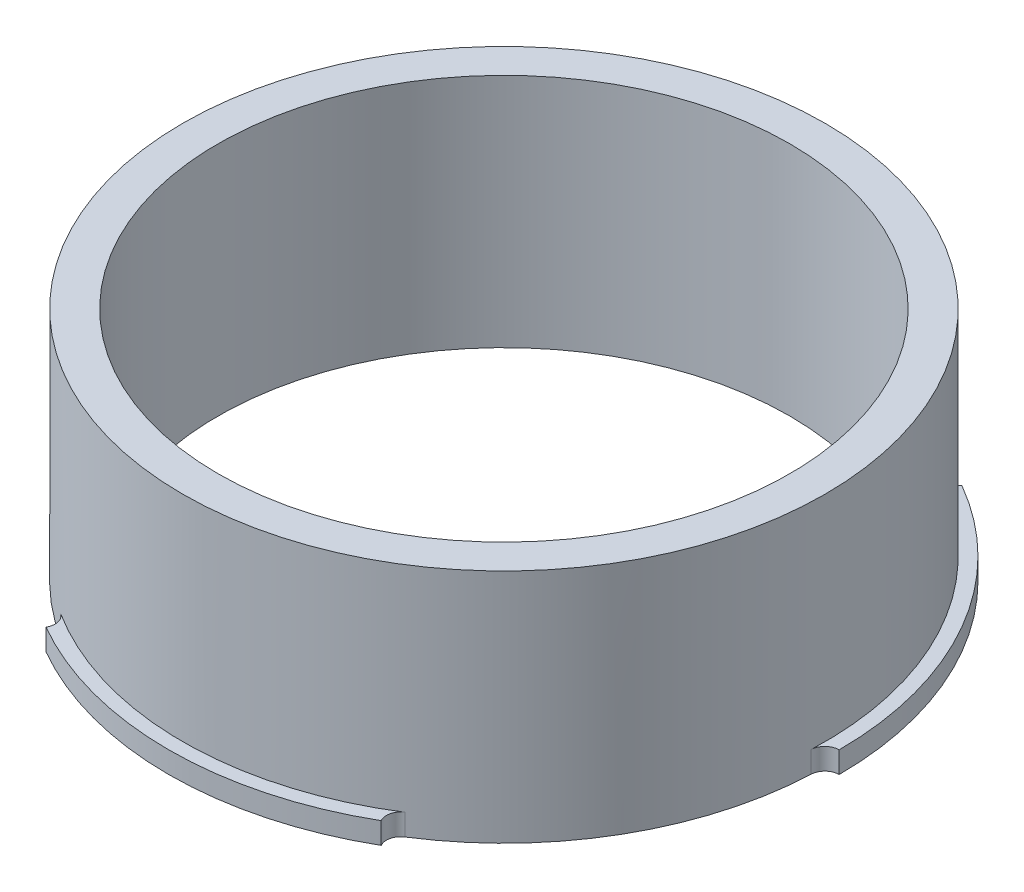
SolidWorks part; units mm, degrees
ref_plane "Front Plane" through (0, 0, 0) normal (0, 0, 1) x (1, 0, 0)
ref_plane "Top Plane" through (0, 0, 0) normal (0, 1, 0) x (1, 0, 0)
ref_plane "Right Plane" through (0, 0, 0) normal (1, 0, 0) x (0, 0, -1)
sketch "Sketch1" plane through (0, 0, 0) normal (0, 1, 0) x (1, 0, 0)
  circle A0 centre (0, 0) radius 20
  circle A1 centre (0, 0) radius 22.475
  dimension "D1" = 40
  dimension "D2" = 44.95
extrude "Boss-Extrude1" add sketch "Sketch1" along normal blind 15
sketch "Sketch2" plane through (0, 0, 0) normal (0, -1, 0) x (1, 0, 0)
  circle A0 centre (0, 0) radius 23.455
  circle A4 centre (0, 0) radius 20 construction
  circle A5 centre (0, 0) radius 20
  dimension "D1" = 46.91
extrude "Boss-Extrude2" add sketch "Sketch2" along normal blind 1.5
sketch "Sketch4" plane through (0, 0, 0) normal (0, 1, 0) x (1, 0, 0)
  line L0 (0, -32.5944) -> (0, 32.5944) construction
  line L1 (-37.1603, 0) -> (37.1603, 0) construction
  line L2 (-11.2375, 19.4639) -> (-11.7275, 20.3126)
  line L3 (11.2375, 19.4639) -> (11.7275, 20.3126)
  circle A0 centre (0, 0) radius 23.455 construction
  arc A1 (11.7275, 20.3126) -> (-11.7275, 20.3126) centre (0, 0) ccw
  circle A2 centre (0, 0) radius 22.475 construction
  arc A3 (11.2375, 19.4639) -> (-11.2375, 19.4639) centre (0, 0) ccw
  point P4 (0, 0)
  point P8 (0, 0)
  dimension "D1" = 30
  dimension "D2" = 30
extrude "Cut-Extrude3" cut sketch "Sketch4" against normal blind 10
pattern_circular "CirPattern1" count 3 over 360 about axis through (0, 0, 0) along (0, 1, 0) of "Cut-Extrude3"
fillet "Fillet1" radius 1 6 edges at (11.2375, -0.75, -19.4639) (-11.2375, -0.75, -19.4639) (-22.475, -0.75, 0) (-11.2375, -0.75, 19.4639) (11.2375, -0.75, 19.4639) (22.475, -0.75, 0)
